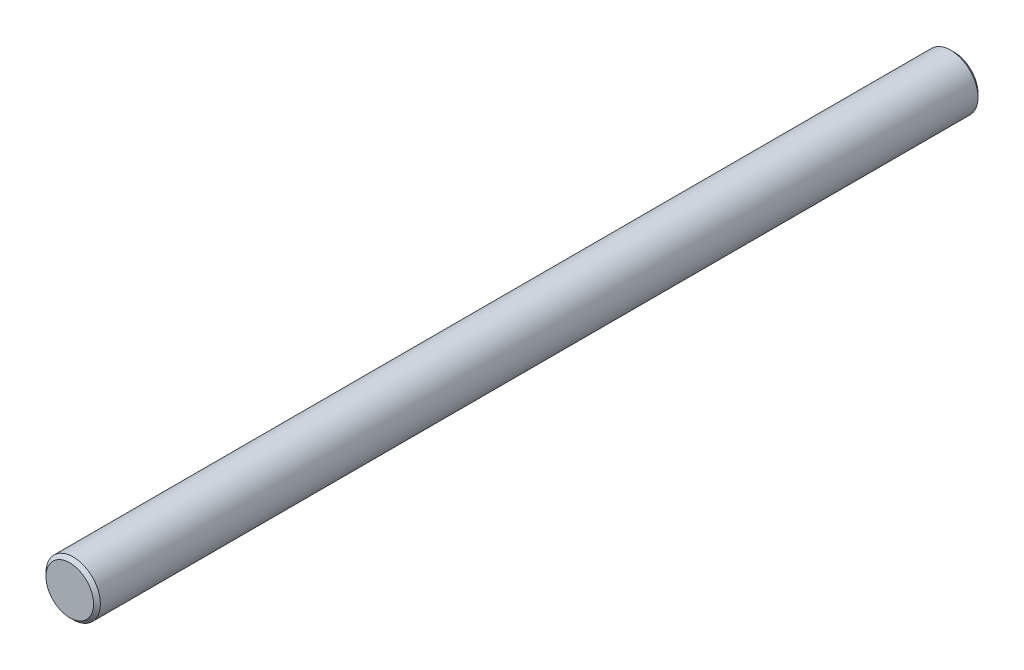
SolidWorks part; units mm, degrees
material "1023 Carbon Steel Sheet (SS)"
ref_plane "Front Plane" through (0, 0, 0) normal (0, 0, 1) x (1, 0, 0)
ref_plane "Top Plane" through (0, 0, 0) normal (0, 1, 0) x (1, 0, 0)
ref_plane "Right Plane" through (0, 0, 0) normal (1, 0, 0) x (0, 0, -1)
sketch "Sketch1" plane through (0, 0, 0) normal (0, 0, 1) x (1, 0, 0)
  circle A0 centre (0, 0) radius 4
  dimension "D1" = 8
extrude "Boss-Extrude1" add sketch "Sketch1" along normal blind 130
chamfer "Chamfer1" distance 0.5 angle 45 2 edges at (4, 0, 0) (4, 0, 130)
